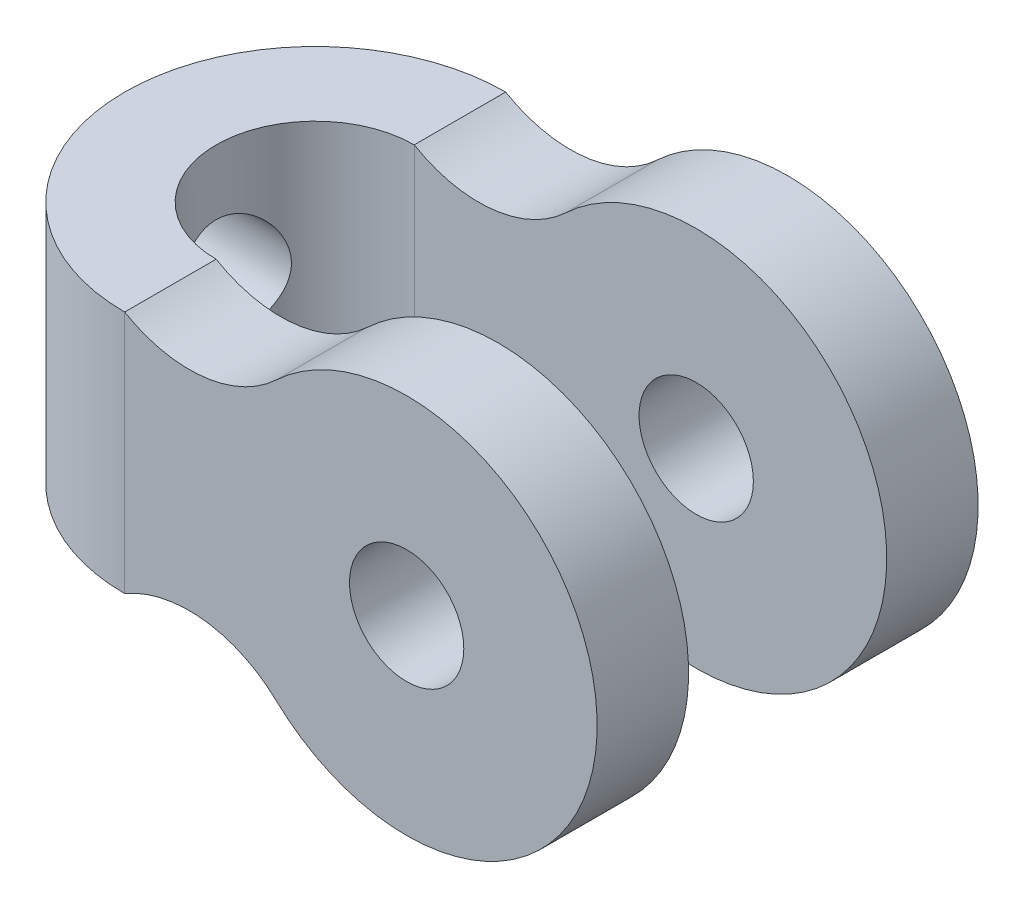
SolidWorks part; units mm, degrees
material "Alloy Steel"
ref_plane "Front Plane" through (0, 0, 0) normal (0, 0, 1) x (1, 0, 0)
ref_plane "Top Plane" through (0, 0, 0) normal (0, 1, 0) x (1, 0, 0)
ref_plane "Right Plane" through (0, 0, 0) normal (1, 0, 0) x (0, 0, -1)
sketch "Sketch1" plane through (0, 0, 0) normal (0, 1, 0) x (1, 0, 0)
  line L0 (0, 25) -> (0, -25)
  arc A0 (0, 25) -> (0, -25) centre (0, 0) ccw
  arc A1 (0, 13) -> (0, -13) centre (0, 0) ccw
  dimension "D1" = 50
  dimension "D2" = 26
extrude "Boss-Extrude1" add sketch "Sketch1" along normal mid plane 32 contours A1 L0 A0
ref_plane "Plane1" through (0, 0, 40) normal (0, 0, 1) x (1, 0, 0)
sketch "Sketch3" plane through (0, 0, 40) normal (0, 0, 1) x (1, 0, 0)
  line L0 (0, 16) -> (0, -16)
  line L2 (0, 16) -> (0, -16) construction
  arc A0 (19.8822, -18.2203) -> (19.8822, 18.2203) centre (37, 0) ccw
  circle A1 centre (37, 0) radius 7.5
  arc A2 (19.8822, 18.2203) -> (0, 16) centre (8.4593, 30.3789) cw
  arc A3 (19.8822, -18.2203) -> (0, -16) centre (8.4593, -30.3789) ccw
  point P5 (19.8822, 18.2203)
  dimension "D1" = 50
  dimension "D2" = 15
  dimension "D3" = 37
extrude "Boss-Extrude2" add sketch "Sketch3" against normal up to vertex (65.001 mm away)
ref_plane "Plane3" through (-40, 0, 0) normal (1, 0, 0) x (0, 0, -1)
sketch "Sketch7" plane through (0, 0, 0) normal (-1, 0, 0) x (0, 0, 1)
  line L0 (40, 25) -> (13, 25) construction
  line L1 (25, 25) -> (40, 25)
  line L2 (25, 25) -> (25, -25)
  line L3 (25, -25) -> (40, -25)
  line L4 (40, 25) -> (40, -25)
extrude "Cut-Extrude1" cut sketch "Sketch7" against normal through all
ref_plane "Plane5" through (0, 0, -25) normal (0, 0, 1) x (1, 0, 0)
sketch "Sketch8" plane through (0, 0, -25) normal (0, 0, 1) x (1, 0, 0)
  line L1 (0, -16) -> (0, 16)
  line L2 (13.75, 0) -> (-13.75, 0) construction
  circle A0 centre (37, 0) radius 7.5
  arc A1 (19.8822, -18.2203) -> (19.8822, 18.2203) centre (37, 0) ccw
  arc A2 (19.8822, -18.2203) -> (0, -16) centre (8.4593, -30.3789) ccw
  arc A3 (19.8822, 18.2203) -> (0, 16) centre (8.4593, 30.3789) cw
  dimension "D1" = 15
extrude "Boss-Extrude6" add sketch "Sketch8" along normal up to vertex (56.8463 mm away)
sketch "Sketch9" plane through (0, 0, 0) normal (1, 0, 0) x (0, 0, -1)
  circle A0 centre (0, 0) radius 7.5
  dimension "D1" = 15
extrude "Cut-Extrude2" cut sketch "Sketch9" against normal through all
